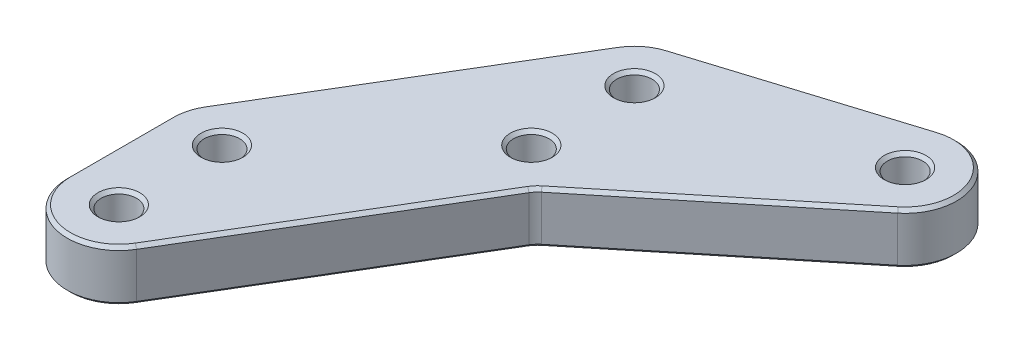
SolidWorks part; units mm, degrees
ref_plane "Front Plane" through (0, 0, 0) normal (0, 0, 1) x (1, 0, 0)
ref_plane "Top Plane" through (0, 0, 0) normal (0, 1, 0) x (1, 0, 0)
ref_plane "Right Plane" through (0, 0, 0) normal (1, 0, 0) x (0, 0, -1)
sketch "Sketch1" plane through (0, 0, 0) normal (0, 1, 0) x (1, 0, 0)
  line L0 (-25.4, -19.05) -> (-25.4, -31.75)
  line L1 (4.5191, -4.8104) -> (-13.6049, -35.017)
  line L2 (-24.4951, -15.783) -> (-5.4451, 15.967)
  line L5 (5.2361, -3.9825) -> (29.411, 15.7147)
  line L6 (-1.894, 18.7609) -> (23.506, 26.6984)
  circle A0 centre (0, 0) radius 2.1828
  circle A1 centre (0, 12.7) radius 2.1828
  circle A2 centre (-19.05, -19.05) radius 2.1828
  circle A3 centre (-19.05, -31.75) radius 2.1828
  arc A4 (-25.4, -31.75) -> (-13.6049, -35.017) centre (-19.05, -31.75) ccw
  arc A5 (-24.4951, -15.783) -> (-25.4, -19.05) centre (-19.05, -19.05) ccw
  arc A7 (-1.894, 18.7609) -> (-5.4451, 15.967) centre (0, 12.7) ccw
  circle A9 centre (25.4, 20.6375) radius 2.1828
  arc A10 (29.411, 15.7147) -> (23.506, 26.6984) centre (25.4, 20.6375) ccw
  arc A12 (4.5191, -4.8104) -> (5.2361, -3.9825) centre (7.2416, -6.4439) cw
  point P19 (4.8051, -4.3337)
  dimension "D2" = 4.3656
  dimension "D3" = 4.3656
  dimension "D6" = 4.3656
  dimension "D8" = 4.3656
  dimension "D9" = 12.7
  dimension "D10" = 4.3337
  dimension "D11" = 12.7
  dimension "D12" = 12.7
  dimension "D15" = 4.3656
  dimension "D16" = 12.7
  dimension "D18" = 3.175
  dimension "D1" = 12.7
  dimension "D4" = 19.05
  dimension "D5" = 19.05
  dimension "D7" = 12.7
  dimension "D13" = 25.4
  dimension "D14" = 7.9375
  dimension "D17" = 4.8051
extrude "Boss-Extrude1" add sketch "Sketch1" along normal mid plane 6.35
chamfer "Chamfer1" distance 0.3969 angle 45 30 edges at (25.4, -3.175, -18.4547) (-19.05, -3.175, 21.2328) (0, -3.175, 2.1828) (17.3236, -3.175, -5.8661) (30.993, -3.175, -23.6444) (10.806, -3.175, -22.7297) (-3.9265, -3.175, -17.6905) (-14.9701, -3.175, -0.092) (-25.1696, -3.175, 17.355) (-25.4, -3.175, 25.4) (-20.745, -3.175, 37.8696) (-4.5429, -3.175, 19.9137) (4.8416, -3.175, 4.3653) (0, -3.175, -10.5172) (-19.05, -3.175, 33.9328) (25.4, 3.175, -18.4547) (-19.05, 3.175, 33.9328) (-19.05, 3.175, 21.2328) (0, 3.175, -10.5172) (0, 3.175, 2.1828) (-4.5429, 3.175, 19.9137) (-20.745, 3.175, 37.8696) (-25.4, 3.175, 25.4) (-25.1696, 3.175, 17.355) (-14.9701, 3.175, -0.092) (-3.9265, 3.175, -17.6905) (10.806, 3.175, -22.7297) (30.993, 3.175, -23.6444) (17.3236, 3.175, -5.8661) (4.8416, 3.175, 4.3653)
